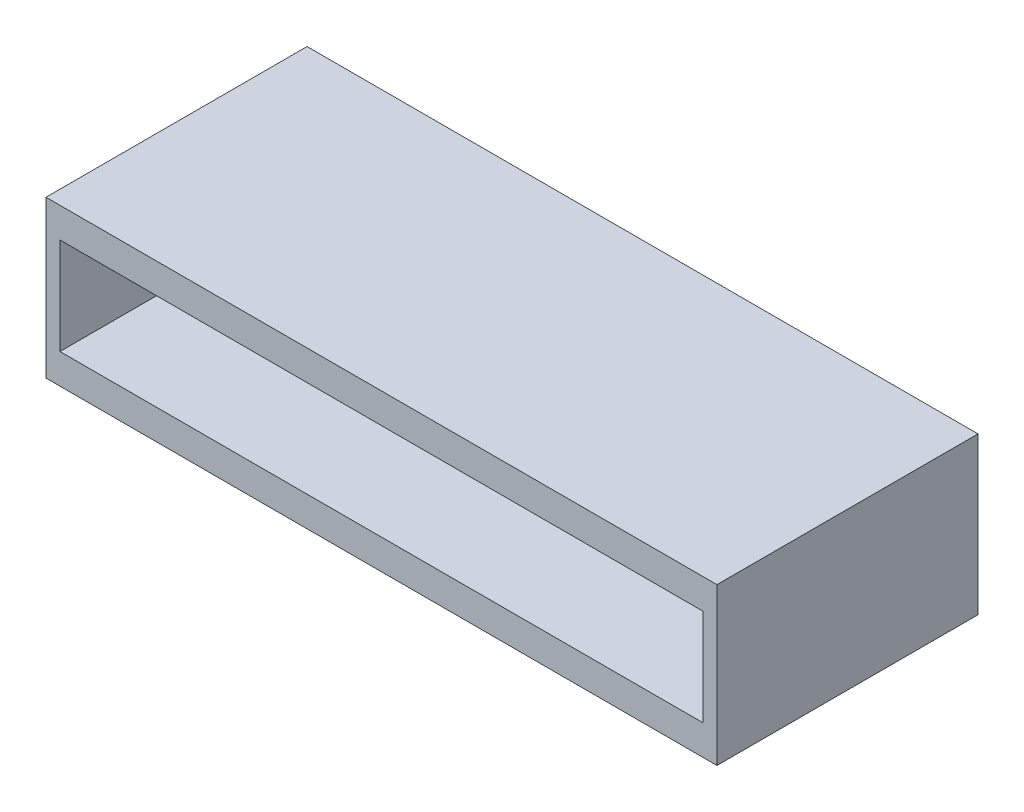
SolidWorks part; units mm, degrees
ref_plane "Front Plane" through (0, 0, 0) normal (0, 0, 1) x (1, 0, 0)
ref_plane "Top Plane" through (0, 0, 0) normal (0, 1, 0) x (1, 0, 0)
ref_plane "Right Plane" through (0, 0, 0) normal (1, 0, 0) x (0, 0, -1)
sketch "Sketch1" plane through (0, 0, 0) normal (0, 1, 0) x (1, 0, 0)
  line L1 (-6.425, 2.5) -> (6.425, 2.5)
  line L2 (-6.425, 2.5) -> (-6.425, -2.5)
  line L3 (-6.425, -2.5) -> (6.425, -2.5)
  line L4 (6.425, 2.5) -> (6.425, -2.5)
  line L5 (-6.425, 2.5) -> (6.425, -2.5) construction
  line L6 (-6.425, -2.5) -> (6.425, 2.5) construction
  point P0 (0, 0)
  dimension "D1" = 12.85
  dimension "D2" = 5
extrude "Boss-Extrude1" add sketch "Sketch1" along normal mid plane 3
sketch "Sketch3" plane through (0, 0, 2.5) normal (0, 0, 1) x (1, 0, 0)
  line L1 (-6.1575, 0.925) -> (6.1575, 0.925)
  line L2 (-6.1575, 0.925) -> (-6.1575, -0.925)
  line L3 (-6.1575, -0.925) -> (6.1575, -0.925)
  line L4 (6.1575, 0.925) -> (6.1575, -0.925)
  line L5 (-6.1575, 0.925) -> (6.1575, -0.925) construction
  line L6 (-6.1575, -0.925) -> (6.1575, 0.925) construction
  point P0 (0, 0)
  dimension "D1" = 1.85
extrude "Cut-Extrude1" cut sketch "Sketch3" against normal blind 3.5
